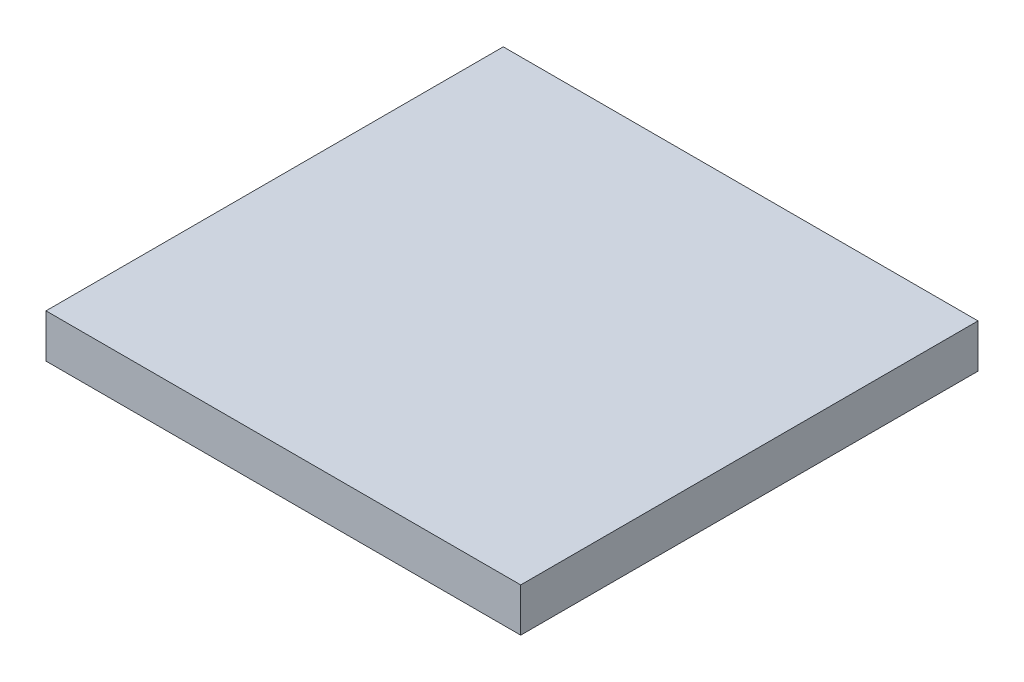
SolidWorks part; units mm, degrees
ref_plane "Front Plane" through (0, 0, 0) normal (0, 0, 1) x (1, 0, 0)
ref_plane "Top Plane" through (0, 0, 0) normal (0, 1, 0) x (1, 0, 0)
ref_plane "Right Plane" through (0, 0, 0) normal (1, 0, 0) x (0, 0, -1)
sketch "Sketch1" plane through (0, 0, 0) normal (0, 1, 0) x (1, 0, 0)
  line L1 (-13.843, -13.335) -> (13.843, -13.335)
  line L2 (-13.843, -13.335) -> (-13.843, 13.335)
  line L3 (-13.843, 13.335) -> (13.843, 13.335)
  line L4 (13.843, -13.335) -> (13.843, 13.335)
  line L5 (-13.843, -13.335) -> (13.843, 13.335) construction
  line L6 (-13.843, 13.335) -> (13.843, -13.335) construction
  point P0 (0, 0)
  dimension "D1" = 27.686
  dimension "D2" = 26.67
extrude "Boss-Extrude1" add sketch "Sketch1" along normal blind 2.54
